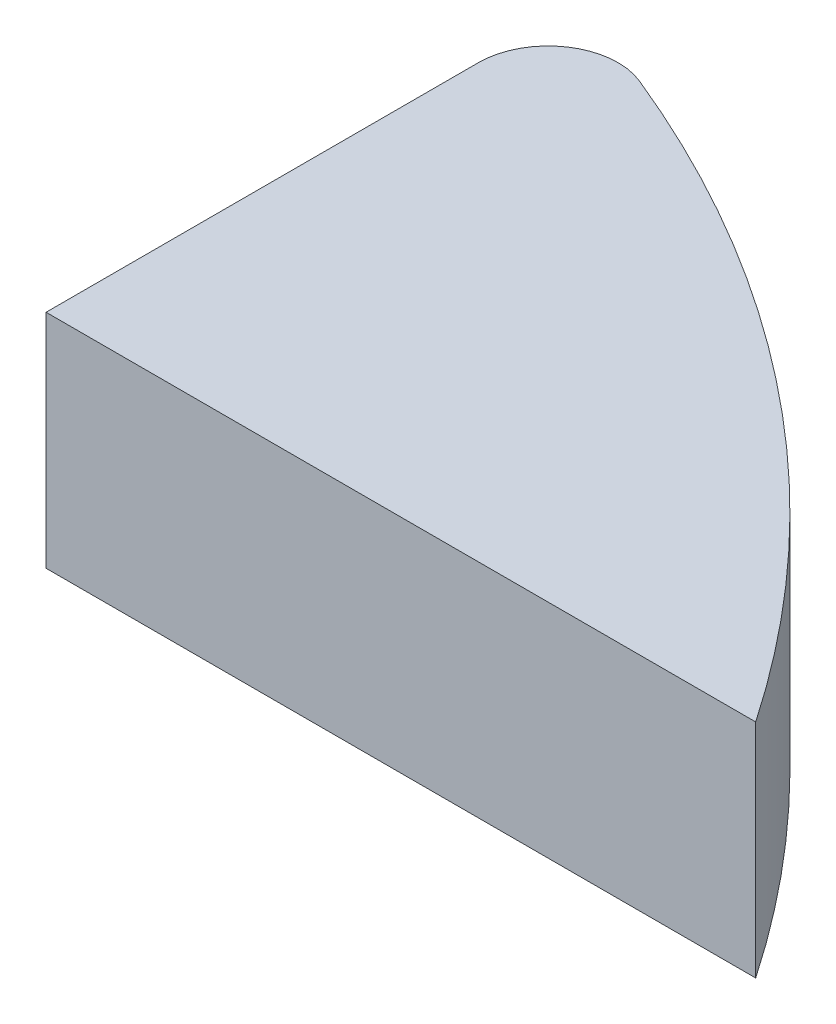
SolidWorks part; units mm, degrees
ref_plane "Front Plane" through (0, 0, 0) normal (0, 0, 1) x (1, 0, 0)
ref_plane "Top Plane" through (0, 0, 0) normal (0, 1, 0) x (1, 0, 0)
ref_plane "Right Plane" through (0, 0, 0) normal (1, 0, 0) x (0, 0, -1)
sketch "Sketch1" plane through (0, 0, 0) normal (0, 1, 0) x (1, 0, 0)
  line L0 (0, 0) -> (0, 15.24)
  line L1 (0, -55) -> (0, 55) construction
  line L2 (0, 0) -> (20.32, 0)
  line L3 (-55, 0) -> (55, 0) construction
  arc A0 (0, 15.24) -> (20.32, 0) centre (-12.0545, -21.9993) cw
extrude "Boss-Extrude1" add sketch "Sketch1" along normal blind 6.35
fillet "Fillet1" radius 2 1 edges at (0, 3.175, -15.24)
